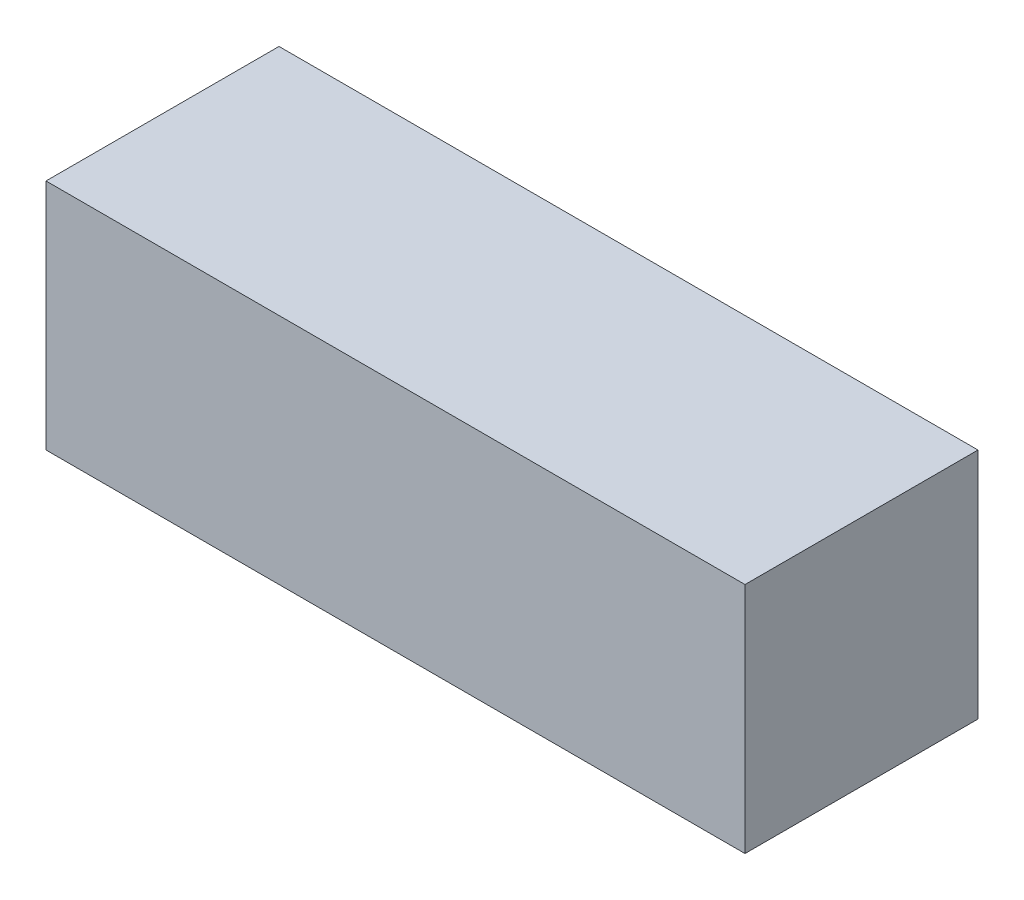
SolidWorks part; units mm, degrees
ref_plane "Спереди" through (0, 0, 0) normal (0, 0, 1) x (1, 0, 0)
ref_plane "Сверху" through (0, 0, 0) normal (0, 1, 0) x (1, 0, 0)
ref_plane "Справа" through (0, 0, 0) normal (1, 0, 0) x (0, 0, -1)
sketch "Эскиз1" plane through (0, 0, 0) normal (1, 0, 0) x (0, 0, -1)
  line L1 (0, 0) -> (10, 0)
  line L2 (0, 0) -> (0, 10)
  line L3 (0, 10) -> (10, 10)
  line L4 (10, 0) -> (10, 10)
extrude "Бобышка-Вытянуть1" add sketch "Эскиз1" along normal blind 30
